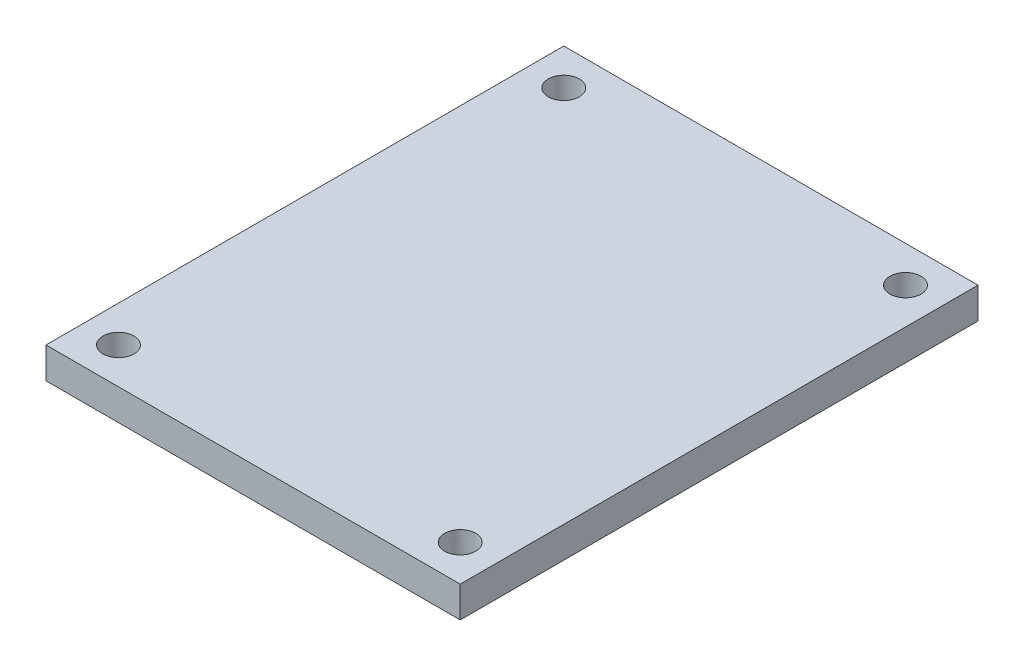
SolidWorks part; units mm, degrees
ref_plane "Alzado" through (0, 0, 0) normal (0, 0, 1) x (1, 0, 0)
ref_plane "Planta" through (0, 0, 0) normal (0, 1, 0) x (1, 0, 0)
ref_plane "Vista lateral" through (0, 0, 0) normal (1, 0, 0) x (0, 0, -1)
sketch "Croquis2" plane through (0, 0, 0) normal (0, 1, 0) x (1, 0, 0)
  line L1 (-254, -317.5) -> (254, -317.5)
  line L2 (-254, -317.5) -> (-254, 317.5)
  line L3 (-254, 317.5) -> (254, 317.5)
  line L4 (254, -317.5) -> (254, 317.5)
  line L5 (-254, -317.5) -> (254, 317.5) construction
  line L6 (-254, 317.5) -> (254, -317.5) construction
  point P0 (0, 0)
  dimension "D1" = 635
  dimension "D2" = 508
extrude "Saliente-Extruir2" add sketch "Croquis2" along normal blind 38.1
sketch "Croquis3" plane through (0, 38.1, 0) normal (0, 1, 0) x (1, 0, 0)
  line L0 (254, 317.5) -> (-254, 317.5) construction
  line L1 (-254, 317.5) -> (-254, -317.5) construction
  line L3 (0, 317.5) -> (0, -317.5) construction
  line L4 (-254, -317.5) -> (254, -317.5) construction
  line L5 (-254, 0) -> (254, 0) construction
  line L6 (254, -317.5) -> (254, 317.5) construction
  circle A0 centre (-209.55, 273.05) radius 19.05
  circle A1 centre (209.55, 273.05) radius 19.05
  circle A2 centre (209.55, -273.05) radius 19.05
  circle A3 centre (-209.55, -273.05) radius 19.05
  dimension "D1" = 38.1
  dimension "D3" = 44.45
  dimension "D2" = 44.45
extrude "Cortar-Extruir1" cut sketch "Croquis3" against normal up to surface (38.1 mm away) up to face at (0, 0, 0)
